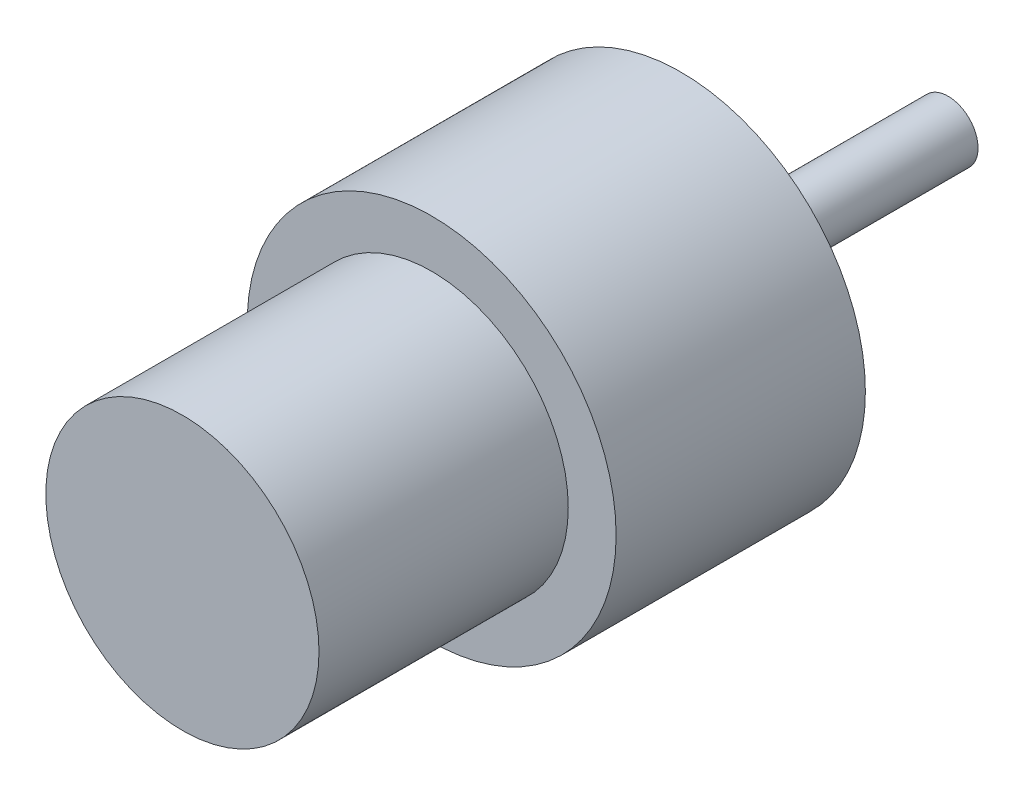
SolidWorks part; units mm, degrees
material "Plain Carbon Steel"
ref_plane "Front Plane" through (0, 0, 0) normal (0, 0, 1) x (1, 0, 0)
ref_plane "Top Plane" through (0, 0, 0) normal (0, 1, 0) x (1, 0, 0)
ref_plane "Right Plane" through (0, 0, 0) normal (1, 0, 0) x (0, 0, -1)
sketch "Sketch1" plane through (0, 0, 0) normal (0, 0, 1) x (1, 0, 0)
  circle A0 centre (0, 0) radius 18.5
  dimension "D1" = 37
extrude "Boss-Extrude1" add sketch "Sketch1" along normal blind 25
sketch "Sketch2" plane through (0, 0, 0) normal (0, 0, -1) x (-1, 0, 0)
  circle A0 centre (0, 0) radius 6
  dimension "D1" = 12
  dimension "D2" = 0
extrude "Boss-Extrude2" add sketch "Sketch2" along normal blind 6.8
sketch "Sketch3" plane through (0, 0, -6.8) normal (0, 0, -1) x (-1, 0, 0)
  circle A0 centre (0, 0) radius 3
extrude "Boss-Extrude3" add sketch "Sketch3" along normal blind 20
sketch "Sketch5" plane through (0, 0, 25) normal (0, 0, 1) x (1, 0, 0)
  circle A0 centre (0, 0) radius 13.7
  dimension "D1" = 27.4
extrude "Boss-Extrude4" add sketch "Sketch5" along normal blind 25
